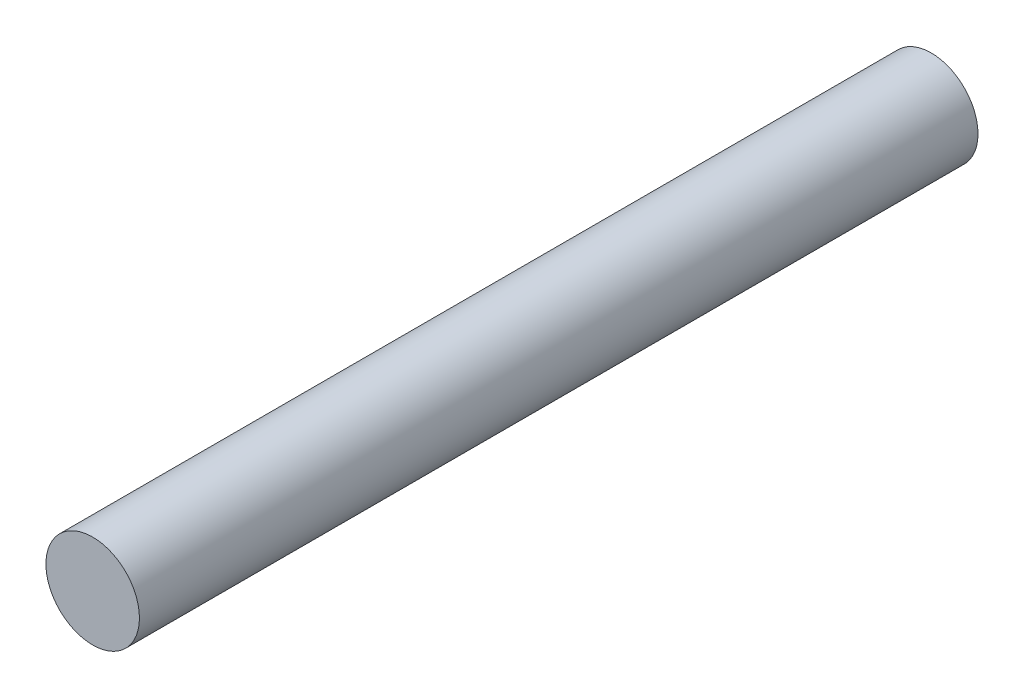
SolidWorks part; units mm, degrees
ref_plane "前视基准面" through (0, 0, 0) normal (0, 0, 1) x (1, 0, 0)
ref_plane "上视基准面" through (0, 0, 0) normal (0, 1, 0) x (1, 0, 0)
ref_plane "右视基准面" through (0, 0, 0) normal (1, 0, 0) x (0, 0, -1)
sketch "草图1" plane through (0, 0, 0) normal (0, 0, 1) x (1, 0, 0)
  circle A0 centre (-7.8955, 14.0705) radius 4
extrude "凸台-拉伸1" add sketch "草图1" along normal blind 71.73
